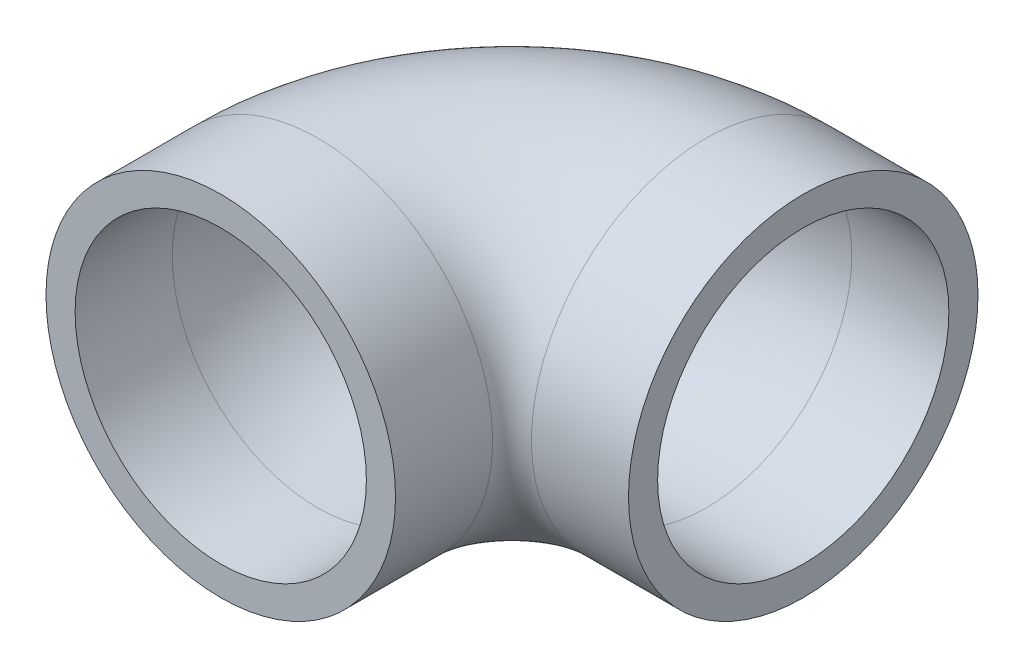
SolidWorks part; units mm, degrees
material "PVC Rigid"
ref_plane "Front Plane" through (0, 0, 0) normal (0, 0, 1) x (1, 0, 0)
ref_plane "Top Plane" through (0, 0, 0) normal (0, 1, 0) x (1, 0, 0)
ref_plane "Right Plane" through (0, 0, 0) normal (1, 0, 0) x (0, 0, -1)
sketch "Sketch1" plane through (0, 0, 0) normal (0, 0, 1) x (1, 0, 0)
  circle A0 centre (0, 0) radius 22.86
  circle A1 centre (0, 0) radius 19.05
  dimension "D1" = 38.1
  dimension "D2" = 45.72
sketch "Sketch3" plane through (0, 0, 0) normal (0, 1, 0) x (1, 0, 0)
  line L0 (0, 0) -> (0, 12.7)
  line L1 (25.4, 38.1) -> (38.1, 38.1)
  arc A0 (0, 12.7) -> (25.4, 38.1) centre (25.4, 12.7) cw
  point P2 (0, 0)
  dimension "D2" = 25.4
  dimension "D1" = 12.7
sweep "Sweep1" add profiles "Sketch1" path "Sketch3"
